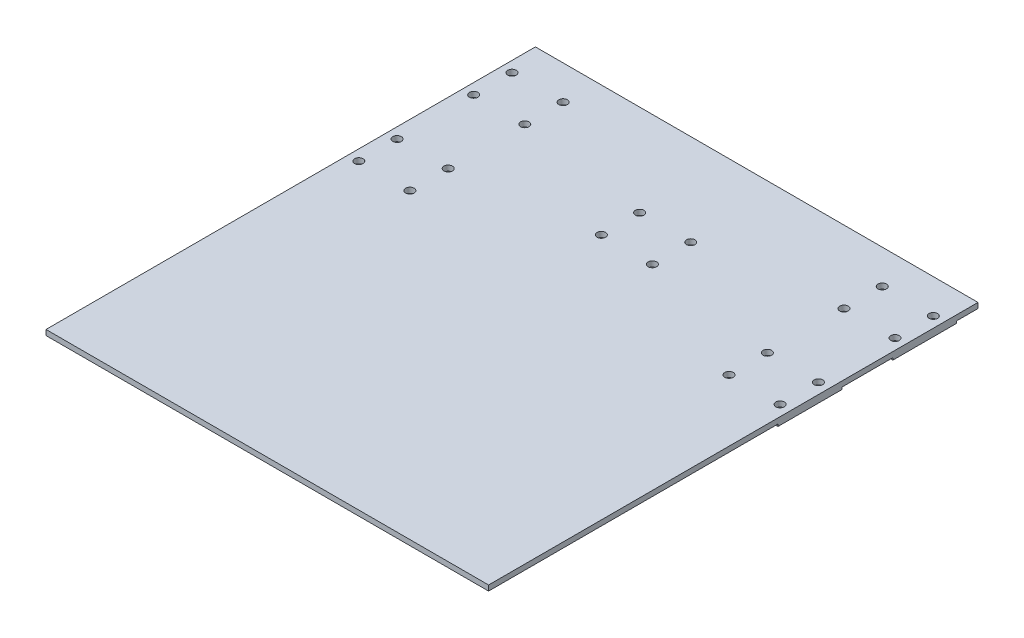
SolidWorks part; units mm, degrees
ref_plane "Alzado" through (0, 0, 0) normal (0, 0, 1) x (1, 0, 0)
ref_plane "Planta" through (0, 0, 0) normal (0, 1, 0) x (1, 0, 0)
ref_plane "Vista lateral" through (0, 0, 0) normal (1, 0, 0) x (0, 0, -1)
sketch "Croquis1" plane through (0, 0, 0) normal (0, 1, 0) x (1, 0, 0)
  line L1 (-104, -182.5) -> (104, -182.5)
  line L2 (-104, -182.5) -> (-104, 182.5)
  line L3 (-104, 182.5) -> (104, 182.5)
  line L4 (104, -182.5) -> (104, 182.5)
  line L5 (-104, -182.5) -> (104, 182.5) construction
  line L6 (-104, 182.5) -> (104, -182.5) construction
  point P0 (0, 0)
  dimension "D1" = 208
  dimension "D2" = 365
extrude "Saliente-Extruir1" add sketch "Croquis1" along normal blind 2.5
sketch "Croquis2" plane through (0, 0, 0) normal (0, -1, 0) x (-1, 0, 0)
  line L0 (87, -182.5) -> (87, 182.5) construction
  line L1 (104, -182.5) -> (-104, -182.5) construction
  line L2 (0, -182.5) -> (0, 182.5) construction
  line L3 (-104, 182.5) -> (104, 182.5) construction
  line L4 (-87, -182.5) -> (-87, 182.5) construction
  line L18 (104, -46.5) -> (70, -46.5)
  line L19 (104, -16.5) -> (104, -46.5)
  line L20 (104, -16.5) -> (70, -16.5)
  line L21 (70, -16.5) -> (70, -46.5)
  line L22 (-70, -16.5) -> (-70, -46.5)
  line L23 (-104, -16.5) -> (-70, -16.5)
  line L24 (-104, -16.5) -> (-104, -46.5)
  line L25 (-104, -46.5) -> (-70, -46.5)
  line L27 (-104, 37.5) -> (-70, 37.5)
  line L28 (-104, 7.5) -> (-104, 37.5)
  line L29 (-104, 7.5) -> (-70, 7.5)
  line L30 (-70, 7.5) -> (-70, 37.5)
  line L31 (70, 7.5) -> (70, 37.5)
  line L32 (104, 7.5) -> (70, 7.5)
  line L33 (104, 7.5) -> (104, 37.5)
  line L34 (104, 37.5) -> (70, 37.5)
  point P10 (70, -45.0557)
  point P11 (0, 0)
  point P12 (-104, -9.5)
  point P13 (-96.7913, 27.5)
  point P14 (-94.9734, 21.9169)
  point P15 (-61.4588, 27.5)
  point P16 (104, -26.5)
  point P17 (102.8477, 27.5)
  point P18 (69.3239, 27.5)
  point P38 (-104, 10)
  dimension "D5" = 34
  dimension "D6" = 30
  dimension "D7" = 34
  dimension "D8" = 30
  dimension "D9" = 24
  dimension "D10" = 17
  dimension "D11" = 34
  dimension "D12" = 70
  dimension "D13" = 70
  dimension "D14" = 30
  dimension "D3" = 30
  dimension "D4" = 166
  dimension "D15" = 34
  dimension "D1" = 87
  dimension "D2" = 87
extrude "Saliente-Extruir2" add sketch "Croquis2" along normal blind 1
sketch "Croquis3" plane through (0, 2.5, 0) normal (0, 1, 0) x (1, 0, 0)
  line L5 (104, -182.5) -> (104, 182.5) construction
  line L6 (-104, 182.5) -> (104, 182.5)
  line L7 (-104, 182.5) -> (-104, 47.5)
  line L8 (-104, 47.5) -> (104, 47.5)
  line L9 (104, 182.5) -> (104, 47.5)
  dimension "D1" = 135
extrude "Cortar-Extruir1" cut sketch "Croquis3" against normal through all
sketch "Sketch1" plane through (0, 0, 0) normal (0, -1, 0) x (1, 0, 0)
  circle A0 centre (-99, 40.5) radius 2
  circle A1 centre (-75, 40.5) radius 2
  circle A2 centre (-99, 22.5) radius 2
  circle A3 centre (-75, 22.5) radius 2
  circle A4 centre (-99, -13.5) radius 2
  circle A5 centre (-99, -31.5) radius 2
  circle A6 centre (-75, -31.5) radius 2
  circle A7 centre (-75, -13.5) radius 2
  circle A8 centre (75, -13.5) radius 2
  circle A9 centre (75, -31.5) radius 2
  circle A10 centre (99, -31.5) radius 2
  circle A11 centre (99, -13.5) radius 2
  circle A12 centre (99, 22.5) radius 2
  circle A13 centre (75, 22.5) radius 2
  circle A14 centre (75, 40.5) radius 2
  circle A15 centre (99, 40.5) radius 2
  circle A16 centre (-12, 13.5) radius 2
  circle A17 centre (-12, -4.5) radius 2
  circle A18 centre (12, -4.5) radius 2
  circle A19 centre (12, 13.5) radius 2
  dimension "D1" = 4
  dimension "D2" = 4
  dimension "D3" = 4
  dimension "D4" = 4
  dimension "D5" = 4
  dimension "D6" = 4
  dimension "D7" = 4
  dimension "D8" = 4
  dimension "D9" = 4
  dimension "D10" = 4
  dimension "D11" = 4
  dimension "D12" = 4
  dimension "D13" = 4
  dimension "D14" = 4
  dimension "D15" = 4
  dimension "D16" = 4
  dimension "D17" = 4
  dimension "D18" = 4
  dimension "D19" = 4
  dimension "D20" = 4
extrude "Cut-Extrude1" cut sketch "Sketch1" against normal up to surface (2.5 mm away) up to face at (0, 2.5, 67.5)
